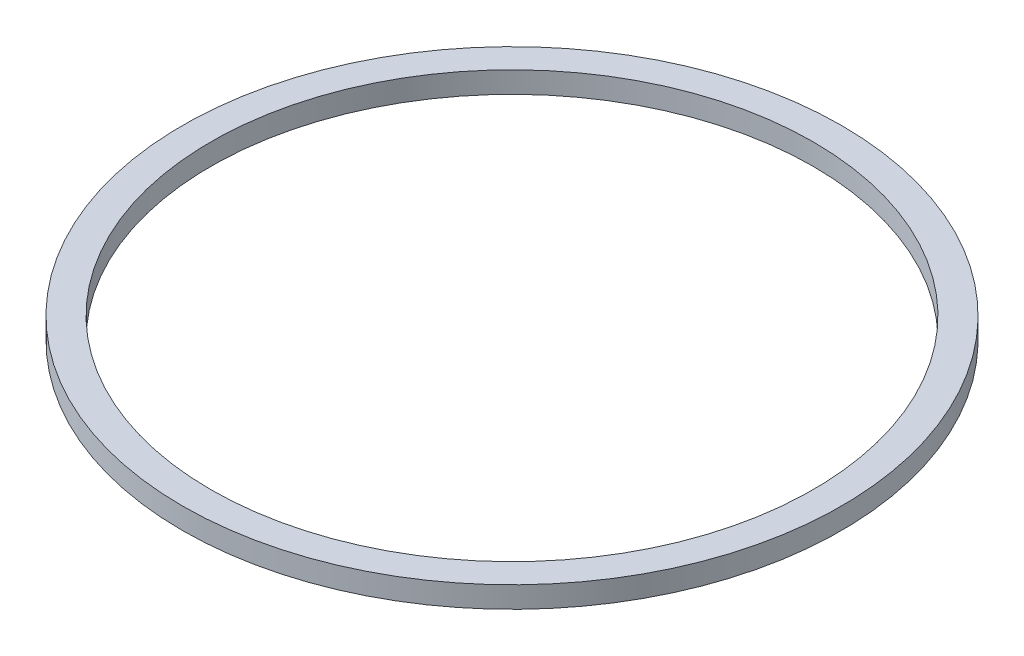
SolidWorks part; units mm, degrees
ref_plane "Front Plane" through (0, 0, 0) normal (0, 0, 1) x (1, 0, 0)
ref_plane "Top Plane" through (0, 0, 0) normal (0, 1, 0) x (1, 0, 0)
ref_plane "Right Plane" through (0, 0, 0) normal (1, 0, 0) x (0, 0, -1)
sketch "Sketch1" plane through (0, 0, 0) normal (0, 1, 0) x (1, 0, 0)
  circle A0 centre (0, 0) radius 42.5
  circle A1 centre (0, 0) radius 46.5
  dimension "D1" = 93
  dimension "D2" = 85
extrude "Boss-Extrude1" add sketch "Sketch1" along normal blind 3
